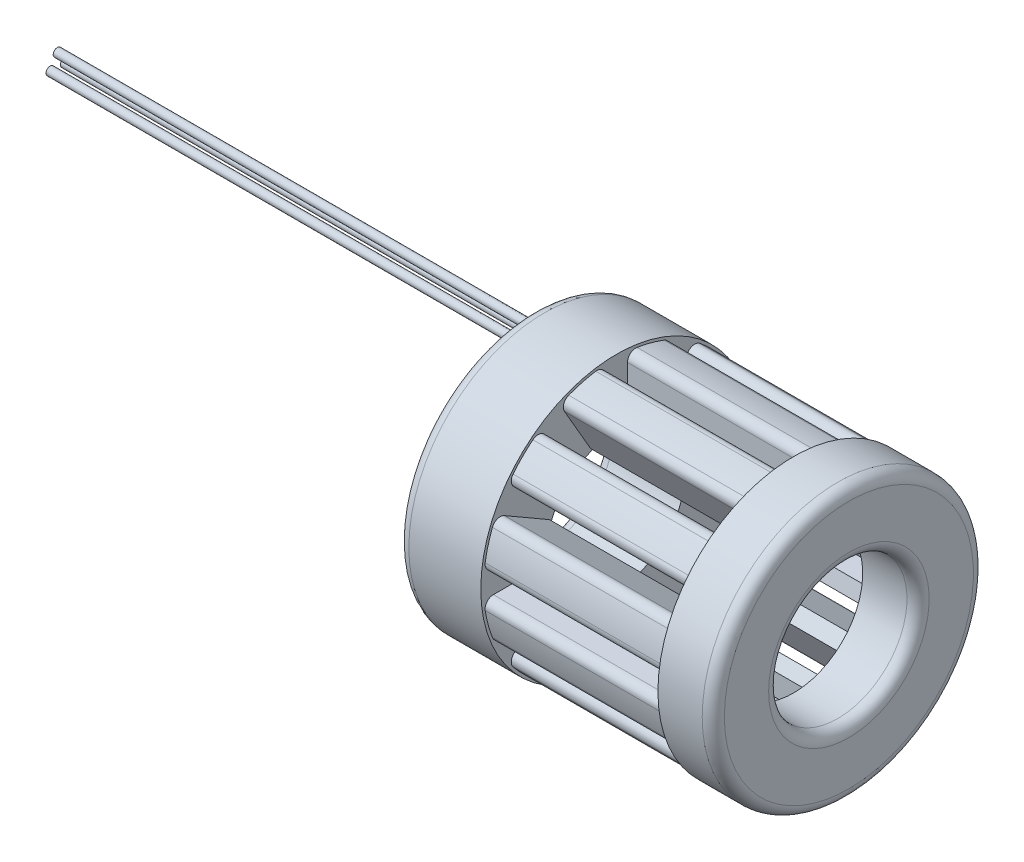
SolidWorks part; units mm, degrees
material "Winding"
ref_plane "Front Plane" through (0, 0, 0) normal (0, 0, 1) x (1, 0, 0)
ref_plane "Top Plane" through (0, 0, 0) normal (0, 1, 0) x (1, 0, 0)
ref_plane "Right Plane" through (0, 0, 0) normal (1, 0, 0) x (0, 0, -1)
sketch "Sketch3" plane through (0, 0, 0) normal (1, 0, 0) x (0, 0, -1)
  line L0 (-14.25, 24.6817) -> (-5.575, 9.6562) construction
  line L1 (0, 28.5) -> (0, 11.15) construction
  line L2 (-1.5, 22.2261) -> (-1.5, 12.8219) construction
  line L3 (-9.814, 19.9984) -> (-5.1119, 11.8541) construction
  line L4 (-1.5, 12.8219) -> (-2.4142, 11.9077) construction
  line L5 (-2.4142, 11.9077) -> (-2.1549, 10.9398) construction
  line L6 (-3.6037, 10.5516) -> (-3.8631, 11.5195) construction
  line L7 (-3.8631, 11.5195) -> (-5.1119, 11.8541) construction
  line L8 (0, 0) -> (-6.4601, 24.1093) construction
  line L9 (-2, 22.2261) -> (-2, 12.8219)
  line L10 (-9.381, 20.2484) -> (-4.6789, 12.1041)
  line L11 (-4.6789, 12.1041) -> (-2, 12.8219)
  arc A0 (0, 28.5) -> (-14.25, 24.6817) centre (0, 0) ccw construction
  arc A1 (0, 11.15) -> (-5.575, 9.6562) centre (0, 0) ccw construction
  arc A2 (-8.8004, 22.8649) -> (-3.8111, 24.2018) centre (0, 0) cw construction
  arc A3 (-5.575, 9.6562) -> (-3.6037, 10.5516) centre (0, 0) cw construction
  arc A4 (-2.1549, 10.9398) -> (0, 11.15) centre (0, 0) cw construction
  arc A5 (-1.5, 22.2261) -> (-3.8111, 24.2018) centre (-3.5, 22.2261) ccw construction
  arc A6 (-8.8004, 22.8649) -> (-9.814, 19.9984) centre (-8.082, 20.9984) ccw construction
  arc A7 (-2.4142, 11.9077) -> (-3.8631, 11.5195) centre (0, 0) ccw construction
  arc A8 (-2, 22.2261) -> (-3.7333, 23.7079) centre (-3.5, 22.2261) ccw
  arc A9 (-8.6208, 22.3983) -> (-3.7333, 23.7079) centre (0, 0) cw
  arc A10 (-8.6208, 22.3983) -> (-9.381, 20.2484) centre (-8.082, 20.9984) ccw
  dimension "D1" = 28.5
  dimension "D2" = 11.15
  dimension "D7" = 2
  dimension "D3" = 30
  dimension "D4" = 1.5
  dimension "D5" = 1.5
  dimension "D6" = 4
  dimension "D8" = 15
  dimension "D9" = 1.5
  dimension "D10" = 0.75
  dimension "D11" = 1
  dimension "D12" = 120
  dimension "D13" = 120
  dimension "D14" = 0.5
extrude "Boss-Extrude1" add sketch "Sketch3" along normal blind 31 and the other way blind 1
ref_axis "Axis1" through (-2, 0, 0) along (1, 0, 0)
sketch "Sketch4" plane through (0, 0, 0) normal (0, 0, 1) x (1, 0, 0)
  line L0 (-2, 0) -> (42, 0) construction
  line L1 (-1, 24.5) -> (-14, 24.5)
  line L2 (-1, 24.5) -> (-1, 12.5)
  line L3 (-1, 12.5) -> (-14, 12.5)
  line L4 (-16, 22.5) -> (-16, 14.5)
  line L5 (31, 24.5) -> (39, 24.5)
  line L6 (31, 24.5) -> (31, 12.5)
  line L7 (31, 12.5) -> (39, 12.5)
  line L8 (41, 22.5) -> (41, 14.5)
  arc A0 (-14, 12.5) -> (-16, 14.5) centre (-14, 14.5) cw
  arc A1 (-14, 24.5) -> (-16, 22.5) centre (-14, 22.5) ccw
  arc A2 (39, 24.5) -> (41, 22.5) centre (39, 22.5) cw
  arc A3 (39, 12.5) -> (41, 14.5) centre (39, 14.5) ccw
  dimension "D1" = 2
  dimension "D2" = 0
  dimension "D3" = 0
  dimension "D4" = 1
  dimension "D5" = 32
  dimension "D6" = 24.5
  dimension "D7" = 10
  dimension "D9" = 12
  dimension "D8" = 15
revolve "Revolve1" add sketch "Sketch4" angle 360 about axis through (-2, 0, 0) along (1, 0, 0)
pattern_circular "CirPattern3" count 12 over 360 about axis through (0, 0, 0) along (1, 0, 0) of "Boss-Extrude1"
sketch "Sketch5" plane through (0, 0, 0) normal (1, 0, 0) x (0, 0, -1)
  line L0 (0, 21.2517) -> (-1.3, 19) construction
  line L1 (-1.3, 19) -> (1.3, 19) construction
  line L2 (1.3, 19) -> (0, 21.2517) construction
  line L3 (0, 21.2517) -> (0, 0) construction
  circle A0 centre (0, 0) radius 19 construction
  circle A1 centre (-1.3, 19) radius 0.75
  circle A2 centre (0, 21.2517) radius 0.75
  circle A3 centre (1.3, 19) radius 0.75
  dimension "D1" = 1.5
  dimension "D2" = 38
  dimension "D3" = 2.6
  dimension "D4" = 2.6
  dimension "D5" = 2.6
extrude "Boss-Extrude2" add sketch "Sketch5" against normal blind 100 from offset 2 contours A2
equation "\"OuterDiam\"= 57"
equation "\"InnerDiam\"= 22.3"
equation "\"Length\"=30"
equation "\"slots\"= 12"
equation "\"ppairs\"= 2"
equation "\"hYoke\"= 4"
equation "\"wTooth\"= 3"
equation "\"D1@Sketch3\"=\"OuterDiam\"/2"
equation "\"D2@Sketch3\"=\"InnerDiam\"/2"
equation "\"D3@Sketch3\"=360deg/\"slots\""
equation "\"D5@Sketch3\"=\"wTooth\"/2"
equation "\"D4@Sketch3\"=\"wTooth\"/2"
equation "\"D6@Sketch3\"=\"hYoke\""
equation "\"D1@Boss-Extrude1\"=\"Length\"+1mm"
equation "\"D8@Sketch3\"= 360deg / \"slots\" / 2"
equation "\"D10@Sketch3\"=\"D9@Sketch3\"/2"
equation "\"D13@Sketch3\"=\"D12@Sketch3\""
equation "\"D1@CirPattern1\"=\"slots\""
equation "\"D1@CirPattern2\"=\"slots\""
equation "\"D5@Sketch4\"=\"Length\"+2mm"
equation "\"D6@Sketch4\"=\"OuterDiam\"/2-\"hYoke\""
equation "\"D1@CirPattern3\"=\"slots\""
equation "\"D3@Sketch5\"=\"D1@Sketch5\"+1.1mm"
equation "\"D4@Sketch5\"=\"D3@Sketch5\""
equation "\"D5@Sketch5\"=\"D3@Sketch5\""
